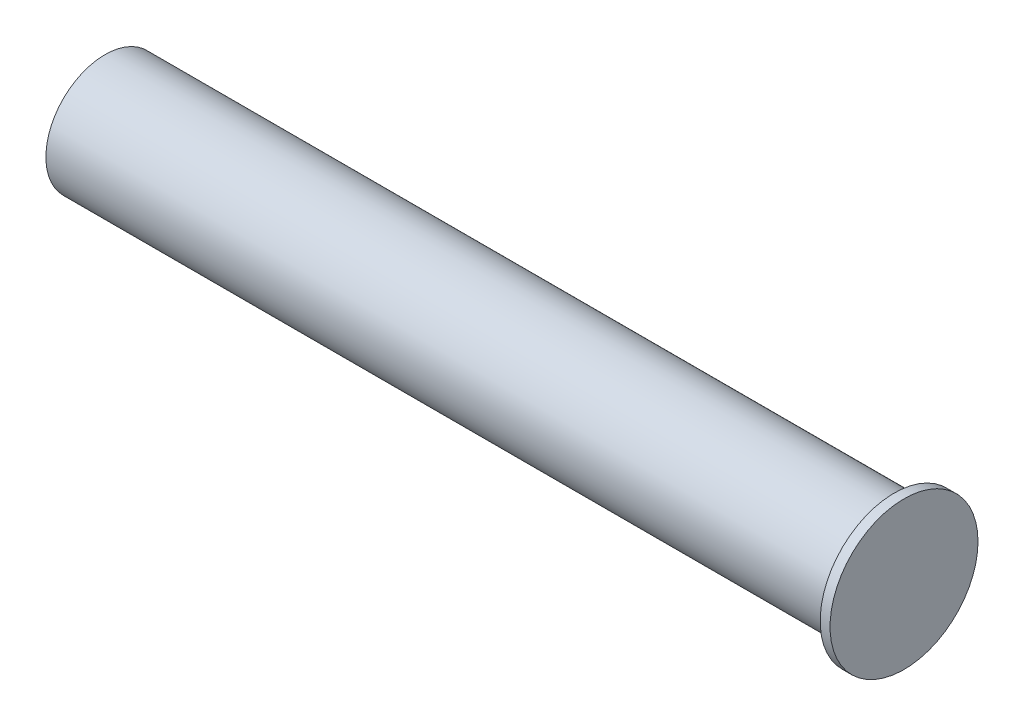
SolidWorks part; units mm, degrees
ref_plane "Front Plane" through (0, 0, 0) normal (0, 0, 1) x (1, 0, 0)
ref_plane "Top Plane" through (0, 0, 0) normal (0, 1, 0) x (1, 0, 0)
ref_plane "Right Plane" through (0, 0, 0) normal (1, 0, 0) x (0, 0, -1)
sketch "Sketch1" plane through (0, 0, 0) normal (1, 0, 0) x (0, 0, -1)
  circle A0 centre (0, 0) radius 6
  dimension "12" = 12
extrude "Boss-Extrude1" add sketch "Sketch1" along normal blind 80
sketch "Sketch2" plane through (80, 0, 0) normal (1, 0, 0) x (0, 0, -1)
  circle A0 centre (0, 0) radius 7.5
  dimension "D1" = 15
extrude "Boss-Extrude2" add sketch "Sketch2" along normal blind 1
